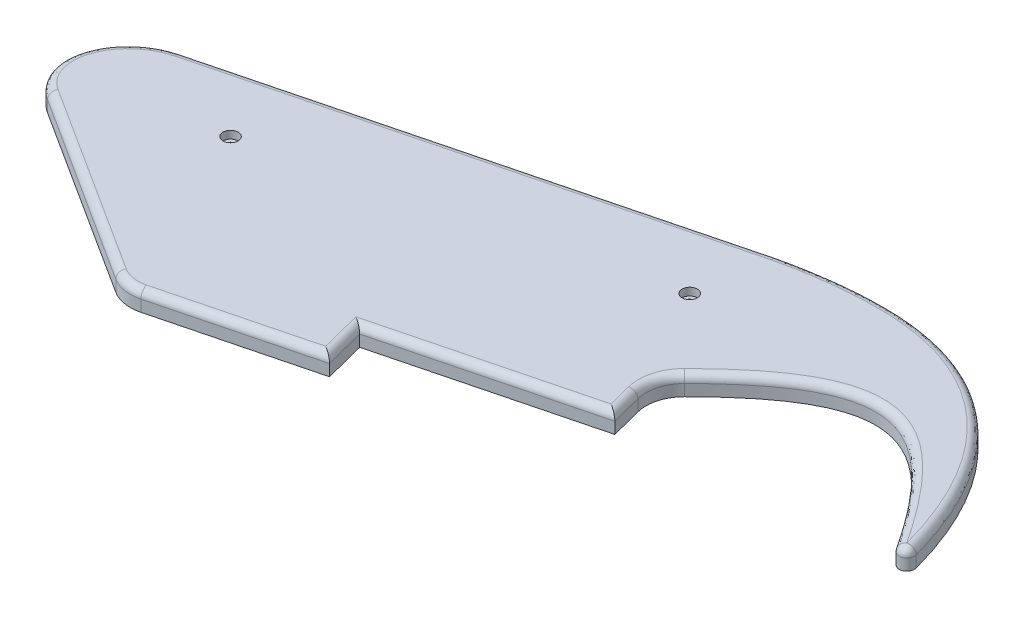
SolidWorks part; units mm, degrees
ref_plane "Front Plane" through (0, 0, 0) normal (0, 0, 1) x (1, 0, 0)
ref_plane "Top Plane" through (0, 0, 0) normal (0, 1, 0) x (1, 0, 0)
ref_plane "Right Plane" through (0, 0, 0) normal (1, 0, 0) x (0, 0, -1)
sketch "Sketch1" plane through (0, 0, 0) normal (0, 1, 0) x (1, 0, 0)
  line L2 (306.7735, -446.0809) -> (304.041, -435.4257)
  line L3 (357.317, -421.763) -> (304.041, -435.4257)
  line L16 (357.317, -421.763) -> (355.2317, -413.6318)
  line L17 (342.6606, -364.6124) -> (218.0874, -396.5594)
  line L18 (209.7913, -423.0919) -> (259.5217, -454.9158)
  line L19 (267.3959, -456.1794) -> (306.7735, -446.0809)
  arc A9 (357.8507, -404.0731) -> (355.2317, -413.6318) centre (364.9183, -411.1477) ccw
  arc A10 (423.6266, -414.2232) -> (427.22, -412.5879) centre (425.2901, -413.113) ccw
  arc A11 (259.5217, -454.9158) -> (267.3959, -456.1794) centre (264.9118, -446.4928) ccw
  spline S6 degree 3 poles (357.8507, -404.0731) (386.4727, -375.4797) (401.109, -380.4819) (423.6266, -414.2232) knots 0.040012 0.040012 0.040012 0.040012 0.916017 0.916017 0.916017 0.916017
  spline S7 degree 3 poles (427.22, -412.5879) (419.1123, -382.7943) (392.6009, -356.8557) (352.6527, -362.299) (342.6606, -364.6124) knots 0.005774 0.005774 0.005774 0.005774 0.670805 1 1 1 1
  spline S8 degree 2 poles (218.0874, -396.5594) (215.9857, -397.0984) (214.0248, -398.1289) (212.0816, -399.1502) (210.4157, -400.582) (208.7354, -402.0262) (207.4596, -403.7842) (206.1524, -405.5855) (205.3693, -407.5798) (204.5435, -409.6828) (204.3684, -411.8262) (204.1845, -414.0763) (204.7341, -416.166) (205.3019, -418.3249) (206.5973, -420.1003) (207.8943, -421.878) (209.7913, -423.0919) knots 0 0 0 0.125 0.125 0.25 0.25 0.375 0.375 0.5 0.5 0.625 0.625 0.75 0.75 0.875 0.875 1 1 1
extrude "Boss-Extrude1" add sketch "Sketch1" along normal blind 5
fillet "Fillet1" radius 2 12 edges at (305.4073, 5, 440.7533) (287.0847, 5, 451.1301) (263.3274, 5, 456.3665) (426.1186, 5, 414.9334) (355.2737, 5, 408.5051) (356.2743, 5, 417.6974) (330.679, 5, 428.5943)
sketch "Sketch2" plane through (0, 0, 0) normal (0, -1, 0) x (1, 0, 0)
  line L0 (242.9227, 409.8052) -> (355.0462, 381.0509) construction
  line L1 (342.6606, 364.6124) -> (218.0874, 396.5594) construction
  circle A0 centre (340.0927, 384.8857) radius 1
  circle A1 centre (244.196, 409.4787) radius 1
  dimension "D1" = 99
  dimension "D2" = 19
  dimension "D3" = 37
extrude "Cut-Extrude1" cut sketch "Sketch2" against normal up to next
sketch "Sketch3" plane through (0, 5, 0) normal (0, 1, 0) x (1, 0, 0)
  circle A0 centre (244.196, -409.4787) radius 2
  circle A1 centre (340.0927, -384.8857) radius 2
extrude "Cut-Extrude2" cut sketch "Sketch3" against normal blind 2
